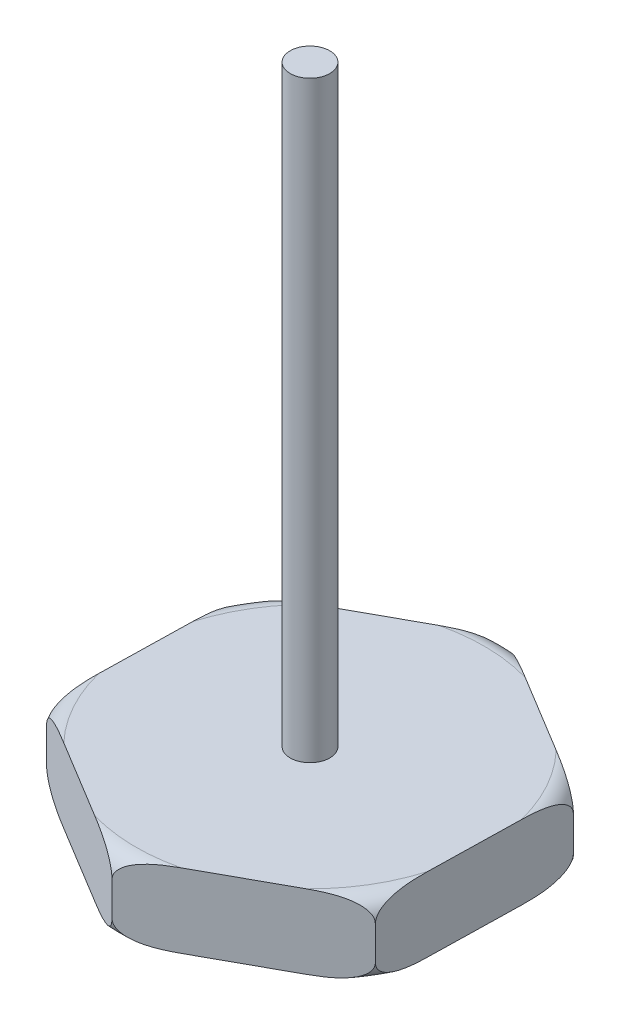
SolidWorks part; units mm, degrees
ref_plane "Front Plane" through (0, 0, 0) normal (0, 0, 1) x (1, 0, 0)
ref_plane "Top Plane" through (0, 0, 0) normal (0, 1, 0) x (1, 0, 0)
ref_plane "Right Plane" through (0, 0, 0) normal (1, 0, 0) x (0, 0, -1)
sketch "Sketch1" plane through (0, 0, 0) normal (0, 1, 0) x (1, 0, 0)
  line L1 (8.6037, 4.7279) -> (0.2073, 9.815)
  line L2 (0.2073, 9.815) -> (-8.3963, 5.087)
  line L3 (-8.3963, 5.087) -> (-8.6037, -4.7279)
  line L4 (-8.6037, -4.7279) -> (-0.2073, -9.815)
  line L5 (-0.2073, -9.815) -> (8.3963, -5.087)
  line L6 (8.3963, -5.087) -> (8.6037, 4.7279)
  dimension "D1" = 17
extrude "Boss-Extrude1" add sketch "Sketch1" along normal mid plane 3.75 contours L4 L5 L6 L1 L2 L3
sketch "Sketch2" plane through (0, 1.875, 0) normal (0, 1, 0) x (1, 0, 0)
  circle A0 centre (0, 0) radius 1
extrude "Boss-Extrude2" add sketch "Sketch2" along normal blind 30
sketch "Sketch3" plane through (0, 0, 0) normal (1, 0, 0) x (0, 0, -1)
  line L0 (-7.639, -1.875) -> (-8.815, -1.875)
  line L2 (-9.815, -1.875) -> (-5.087, -1.875) construction
  line L3 (-9.815, -0.875) -> (-9.815, -0.2367)
  line L5 (-9.815, 1.875) -> (-9.815, -1.875) construction
  line L6 (-9.815, -0.2367) -> (-12.6901, -2.588)
  line L7 (-12.6901, -2.588) -> (-8.5388, -3.3915)
  line L8 (-8.5388, -3.3915) -> (-7.639, -1.875)
  line L9 (-9.815, 0.3423) -> (-9.815, 0.875)
  line L10 (-8.815, 1.875) -> (-7.8199, 1.875)
  line L11 (-9.815, 1.875) -> (-5.087, 1.875) construction
  line L12 (-7.8199, 1.875) -> (-11.7549, 3.8269)
  line L13 (-11.7549, 3.8269) -> (-9.815, 0.3423)
  line L14 (0, 0) -> (0, -2.588) construction
  arc A0 (-8.815, -1.875) -> (-9.815, -0.875) centre (-8.815, -0.875) cw
  arc A1 (-9.815, 0.875) -> (-8.815, 1.875) centre (-8.815, 0.875) cw
  point P19 (-9.815, -1.875)
  point P22 (-9.815, 1.875)
  dimension "D1" = 1
revolve "Cut-Revolve1" cut sketch "Sketch3" angle 360 about L14
